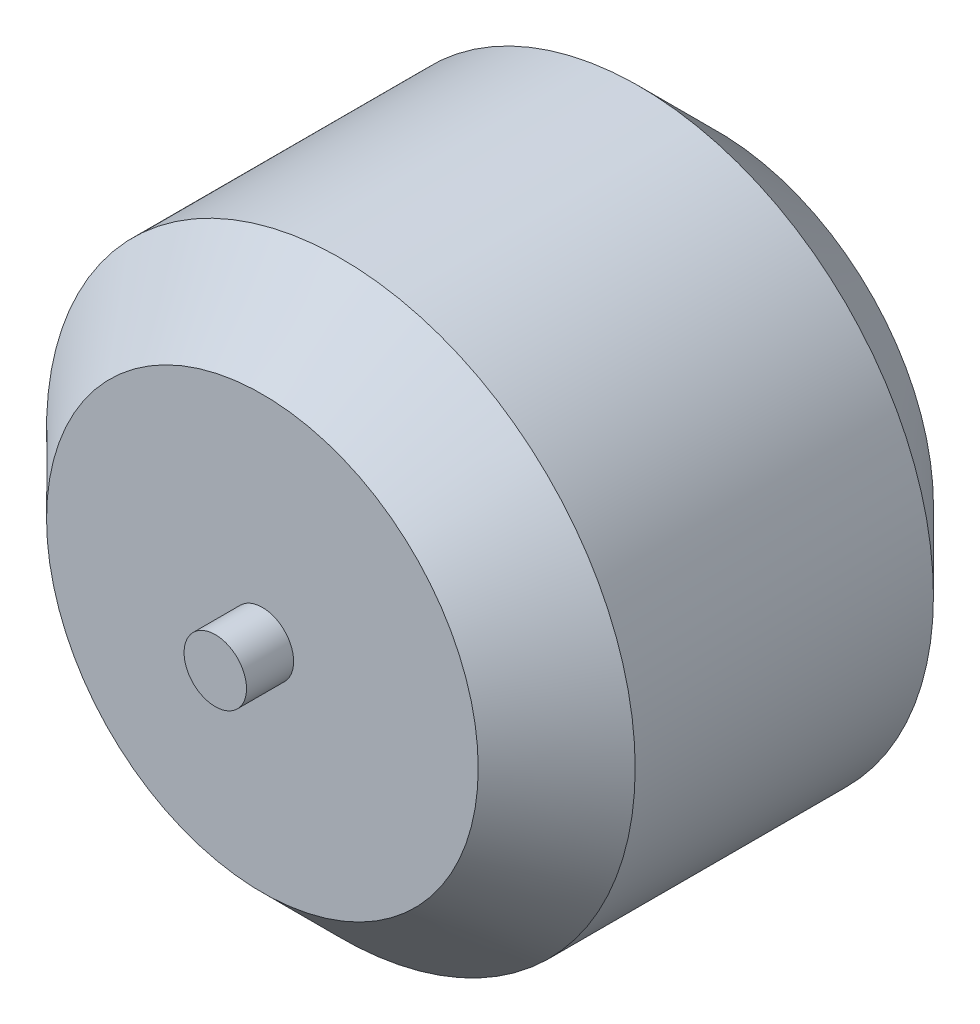
SolidWorks part; units mm, degrees
ref_plane "Plan de face" through (0, 0, 0) normal (0, 0, 1) x (1, 0, 0)
ref_plane "Plan de dessus" through (0, 0, 0) normal (0, 1, 0) x (1, 0, 0)
ref_plane "Plan de droite" through (0, 0, 0) normal (1, 0, 0) x (0, 0, -1)
sketch "Sketch1" plane through (0, 0, 0) normal (0, 0, 1) x (1, 0, 0)
  circle A0 centre (0, 0) radius 18.75
  dimension "D1" = 37.5
extrude "Boss-Extrude1" add sketch "Sketch1" along normal blind 29
sketch "Sketch3" plane through (0, 0, 29) normal (0, 0, 1) x (1, 0, 0)
  circle A0 centre (0, 0) radius 1.99
  dimension "D1" = 3.98
extrude "Boss-Extrude4" add sketch "Sketch3" along normal blind 3
chamfer "Chamfer1" distance 5 angle 45 2 edges at (18.75, 0, 0) (18.75, 0, 29)
sketch "Sketch4" plane through (0, 0, 0) normal (0, 0, -1) x (-1, 0, 0)
  circle A0 centre (0, 0) radius 1.99
  dimension "D1" = 3.98
extrude "Boss-Extrude5" add sketch "Sketch4" along normal blind 1
sketch "Sketch5" plane through (0, 0, 0) normal (0, 0, -1) x (-1, 0, 0)
  circle A0 centre (0, 8) radius 1.5
  point P2 (1.6067, 7.837)
  dimension "D1" = 3
  dimension "D2" = 8
extrude "Cut-Extrude1" cut sketch "Sketch5" against normal blind 1
pattern_circular "CirPattern1" count 4 over 360 about axis through (0, 0, 0) along (0, 0, 1) of "Cut-Extrude1"
